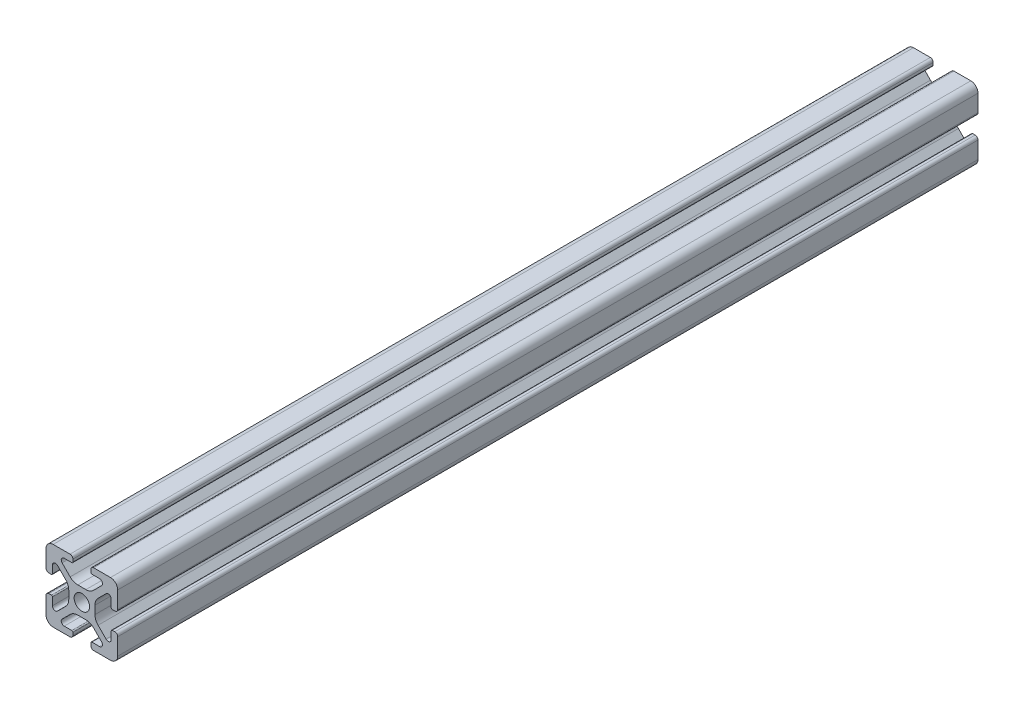
SolidWorks part; units mm, degrees
ref_plane "Front Plane" through (0, 0, 0) normal (0, 0, 1) x (1, 0, 0)
ref_plane "Top Plane" through (0, 0, 0) normal (0, 1, 0) x (1, 0, 0)
ref_plane "Right Plane" through (0, 0, 0) normal (1, 0, 0) x (0, 0, -1)
ref_plane "Plane1" through (0, 0, 0) normal (0, 0, -1) x (-1, 0, 0)
sketch "Sketch1" plane through (0, 0, 0) normal (0, 0, -1) x (-1, 0, 0)
  line L0 (-12.5, 0.8) -> (-12.5, 1.5)
  line L1 (-12.8, 1.8) -> (-14.9176, 1.8)
  line L2 (-15.5062, 3.221) -> (-13.2559, 5.4713)
  line L3 (-11.1346, 6.35) -> (-8.8654, 6.35)
  line L4 (-6.7441, 5.4713) -> (-4.4938, 3.221)
  line L5 (-5.0824, 1.8) -> (-7.2, 1.8)
  line L6 (-7.5, 1.5) -> (-7.5, 0.8)
  line L7 (-6.7, 0) -> (-2, 0)
  line L8 (0, 2) -> (0, 6.7)
  line L9 (-0.8, 7.5) -> (-1.5, 7.5)
  line L10 (-1.8, 7.2) -> (-1.8, 5.0824)
  line L11 (-3.221, 4.4938) -> (-5.4713, 6.7441)
  line L12 (-6.35, 8.8654) -> (-6.35, 11.1346)
  line L13 (-5.4713, 13.2559) -> (-3.221, 15.5062)
  line L14 (-1.8, 14.9176) -> (-1.8, 12.8)
  line L15 (-1.5, 12.5) -> (-0.8, 12.5)
  line L16 (0, 13.3) -> (0, 18)
  line L17 (-2, 20) -> (-6.7, 20)
  line L18 (-7.5, 19.2) -> (-7.5, 18.5)
  line L19 (-7.2, 18.2) -> (-5.0824, 18.2)
  line L20 (-4.4938, 16.779) -> (-6.7441, 14.5287)
  line L21 (-8.8654, 13.65) -> (-11.1346, 13.65)
  line L22 (-13.2559, 14.5287) -> (-15.5062, 16.779)
  line L23 (-14.9176, 18.2) -> (-12.8, 18.2)
  line L24 (-12.5, 18.5) -> (-12.5, 19.2)
  line L25 (-13.3, 20) -> (-18, 20)
  line L26 (-20, 18) -> (-20, 13.3)
  line L27 (-19.2, 12.5) -> (-18.5, 12.5)
  line L28 (-18.2, 12.8) -> (-18.2, 14.9176)
  line L29 (-16.779, 15.5062) -> (-14.5287, 13.2559)
  line L30 (-13.65, 11.1346) -> (-13.65, 8.8654)
  line L31 (-14.5287, 6.7441) -> (-16.779, 4.4938)
  line L32 (-18.2, 5.0824) -> (-18.2, 7.2)
  line L33 (-18.5, 7.5) -> (-19.2, 7.5)
  line L34 (-20, 6.7) -> (-20, 2)
  line L35 (-18, 0) -> (-13.3, 0)
  arc A0 (-12.5, 1.5) -> (-12.8, 1.8) centre (-12.8, 1.5) ccw
  arc A1 (-14.9176, 1.8) -> (-15.5062, 3.221) centre (-14.9176, 2.6324) cw
  arc A2 (-13.2559, 5.4713) -> (-11.1346, 6.35) centre (-11.1346, 3.35) cw
  arc A3 (-8.8654, 6.35) -> (-6.7441, 5.4713) centre (-8.8654, 3.35) cw
  arc A4 (-4.4938, 3.221) -> (-5.0824, 1.8) centre (-5.0824, 2.6324) cw
  arc A5 (-7.2, 1.8) -> (-7.5, 1.5) centre (-7.2, 1.5) ccw
  arc A6 (-7.5, 0.8) -> (-6.7, 0) centre (-6.7, 0.8) ccw
  arc A7 (-2, 0) -> (0, 2) centre (-2, 2) ccw
  arc A8 (0, 6.7) -> (-0.8, 7.5) centre (-0.8, 6.7) ccw
  arc A9 (-1.5, 7.5) -> (-1.8, 7.2) centre (-1.5, 7.2) ccw
  arc A10 (-1.8, 5.0824) -> (-3.221, 4.4938) centre (-2.6324, 5.0824) cw
  arc A11 (-5.4713, 6.7441) -> (-6.35, 8.8654) centre (-3.35, 8.8654) cw
  arc A12 (-6.35, 11.1346) -> (-5.4713, 13.2559) centre (-3.35, 11.1346) cw
  arc A13 (-3.221, 15.5062) -> (-1.8, 14.9176) centre (-2.6324, 14.9176) cw
  arc A14 (-1.8, 12.8) -> (-1.5, 12.5) centre (-1.5, 12.8) ccw
  arc A15 (-0.8, 12.5) -> (0, 13.3) centre (-0.8, 13.3) ccw
  arc A16 (0, 18) -> (-2, 20) centre (-2, 18) ccw
  arc A17 (-6.7, 20) -> (-7.5, 19.2) centre (-6.7, 19.2) ccw
  arc A18 (-7.5, 18.5) -> (-7.2, 18.2) centre (-7.2, 18.5) ccw
  arc A19 (-5.0824, 18.2) -> (-4.4938, 16.779) centre (-5.0824, 17.3676) cw
  arc A20 (-6.7441, 14.5287) -> (-8.8654, 13.65) centre (-8.8654, 16.65) cw
  arc A21 (-11.1346, 13.65) -> (-13.2559, 14.5287) centre (-11.1346, 16.65) cw
  arc A22 (-15.5062, 16.779) -> (-14.9176, 18.2) centre (-14.9176, 17.3676) cw
  arc A23 (-12.8, 18.2) -> (-12.5, 18.5) centre (-12.8, 18.5) ccw
  arc A24 (-12.5, 19.2) -> (-13.3, 20) centre (-13.3, 19.2) ccw
  arc A25 (-18, 20) -> (-20, 18) centre (-18, 18) ccw
  arc A26 (-20, 13.3) -> (-19.2, 12.5) centre (-19.2, 13.3) ccw
  arc A27 (-18.5, 12.5) -> (-18.2, 12.8) centre (-18.5, 12.8) ccw
  arc A28 (-18.2, 14.9176) -> (-16.779, 15.5062) centre (-17.3676, 14.9176) cw
  arc A29 (-14.5287, 13.2559) -> (-13.65, 11.1346) centre (-16.65, 11.1346) cw
  arc A30 (-13.65, 8.8654) -> (-14.5287, 6.7441) centre (-16.65, 8.8654) cw
  arc A31 (-16.779, 4.4938) -> (-18.2, 5.0824) centre (-17.3676, 5.0824) cw
  arc A32 (-18.2, 7.2) -> (-18.5, 7.5) centre (-18.5, 7.2) ccw
  arc A33 (-19.2, 7.5) -> (-20, 6.7) centre (-19.2, 6.7) ccw
  arc A34 (-20, 2) -> (-18, 0) centre (-18, 2) ccw
  arc A35 (-13.3, 0) -> (-12.5, 0.8) centre (-13.3, 0.8) ccw
  circle A36 centre (-10, 10) radius 2.15
extrude "Boss-Extrude1" add sketch "Sketch1" against normal blind 240
equation "\"plate_thickness\" = 6.35 'thickness of the plate "
equation "\"t_height\" = 180"
equation "\"t_width\" = 240"
equation "\"t_length\" = 240"
equation "\"D1@Boss-Extrude1\"=\"t_width\""
